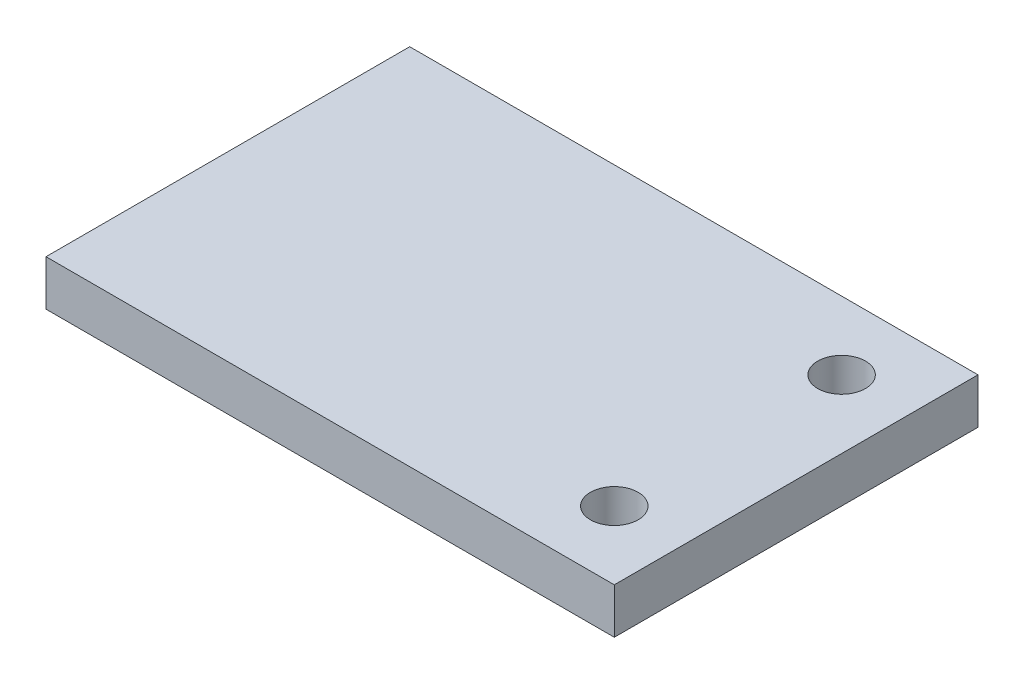
SolidWorks part; units mm, degrees
ref_plane "Front Plane" through (0, 0, 0) normal (0, 0, 1) x (1, 0, 0)
ref_plane "Top Plane" through (0, 0, 0) normal (0, 1, 0) x (1, 0, 0)
ref_plane "Right Plane" through (0, 0, 0) normal (1, 0, 0) x (0, 0, -1)
sketch "Sketch1" plane through (0, 0, 0) normal (0, 1, 0) x (1, 0, 0)
  line L1 (0, 0) -> (50, 0) construction
  line L2 (0, 0) -> (0, 50) construction
  line L3 (0, 50) -> (50, 50) construction
  line L4 (50, 0) -> (50, 50) construction
  line L5 (-10, -15) -> (115, -15)
  line L6 (-10, -15) -> (-10, 65)
  line L7 (-10, 65) -> (115, 65)
  line L8 (115, -15) -> (115, 65)
  line L9 (50, 0) -> (100, 0) construction
  line L10 (50, 0) -> (50, 50) construction
  line L11 (50, 50) -> (100, 50) construction
  line L12 (100, 0) -> (100, 50) construction
  circle A0 centre (100, 50) radius 5.25
  circle A1 centre (100, 0) radius 5.25
  dimension "D6" = 10.5
  dimension "D1" = 50
  dimension "D2" = 15
  dimension "D3" = 15
  dimension "D4" = 10
  dimension "D5" = 50
  dimension "D7" = 15
extrude "Boss-Extrude1" add sketch "Sketch1" along normal blind 10
